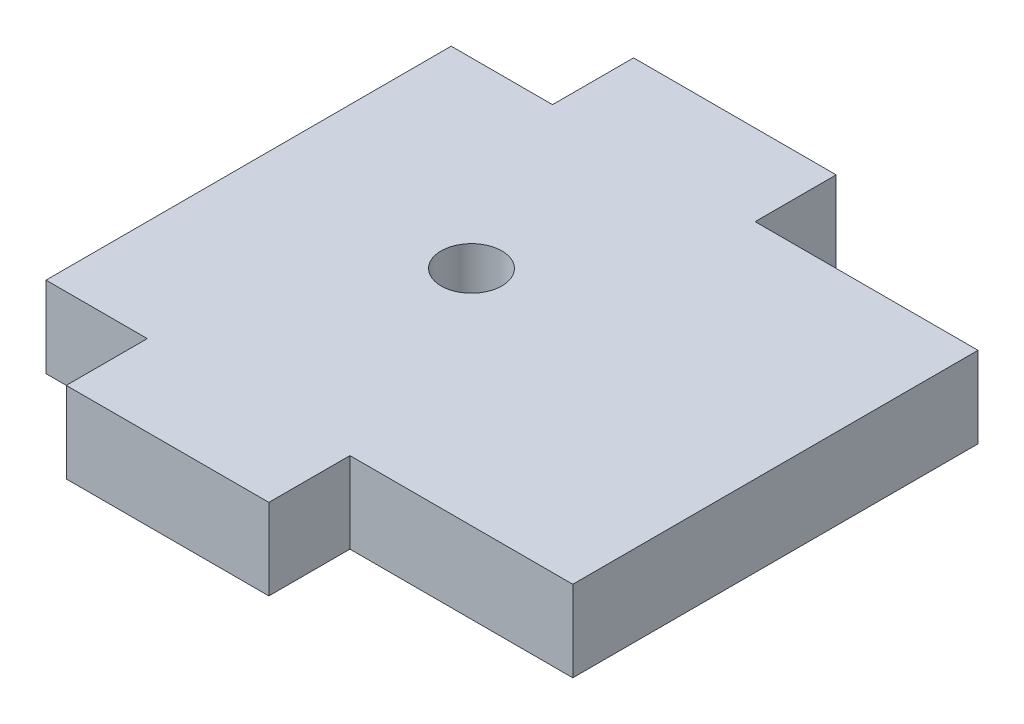
SolidWorks part; units mm, degrees
ref_plane "Front Plane" through (0, 0, 0) normal (0, 0, 1) x (1, 0, 0)
ref_plane "Top Plane" through (0, 0, 0) normal (0, 1, 0) x (1, 0, 0)
ref_plane "Right Plane" through (0, 0, 0) normal (1, 0, 0) x (0, 0, -1)
sketch "Sketch1" plane through (0, 0, 0) normal (0, 1, 0) x (1, 0, 0)
  line L0 (15, 20) -> (26, 20)
  line L5 (0, 0) -> (5, 0)
  line L6 (0, 0) -> (0, 20)
  line L7 (0, 20) -> (5, 20)
  line L8 (26, 0) -> (26, 20)
  line L18 (5, 20) -> (5, 24)
  line L19 (5, 24) -> (15, 24)
  line L20 (15, 20) -> (15, 24)
  line L22 (5, 0) -> (5, -4)
  line L23 (5, -4) -> (15, -4)
  line L24 (15, 0) -> (15, -4)
  line L25 (15, 0) -> (26, 0)
  line L26 (10, 24) -> (10, -2) construction
  line L27 (0, 10) -> (26, 10) construction
  circle A0 centre (10, 11) radius 1.5
  dimension "D1" = 4
  dimension "D2" = 10
  dimension "D3" = 26
  dimension "D4" = 20
  dimension "D5" = 5
  dimension "D6" = 5
  dimension "D7" = 10
  dimension "D8" = 4
extrude "Boss-Extrude2" add sketch "Sketch1" along normal blind 4
